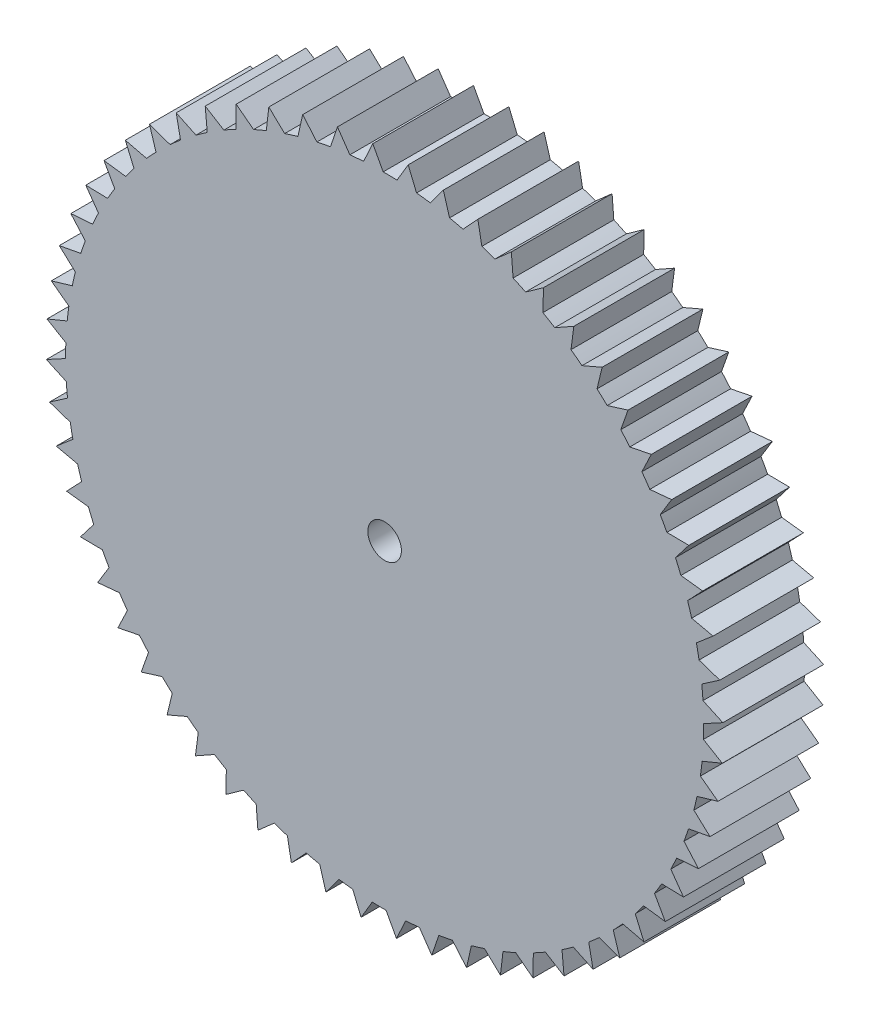
SolidWorks part; units mm, degrees
ref_plane "Front Plane" through (0, 0, 0) normal (0, 0, 1) x (1, 0, 0)
ref_plane "Top Plane" through (0, 0, 0) normal (0, 1, 0) x (1, 0, 0)
ref_plane "Right Plane" through (0, 0, 0) normal (1, 0, 0) x (0, 0, -1)
sketch "Sketch2" plane through (0, 0, 0) normal (0, 1, 0) x (1, 0, 0)
  line L1 (0, 19.1406) -> (0, 42.1406)
  line L2 (21.9625, 25.9706) -> (-21.9625, 25.9706)
  circle A0 centre (0, 19.1406) radius 23
  point P1 (0, 25.9706)
  point P7 (0, 25.9706)
  dimension "D1" = 16.17
  dimension "D2" = 46
ref_plane "Plane1" through (0, 0, -25.9706) normal (0, 0, -1) x (-1, 0, 0)
sketch "Sketch3" plane through (0, 0, -25.9706) normal (0, 0, -1) x (-1, 0, 0)
  line L0 (21.9625, 0) -> (-21.9625, 0)
  line L1 (21.9625, 0) -> (21.9625, 85)
  line L2 (-21.9625, 0) -> (-21.9625, 85)
  line L3 (21.9625, 85) -> (-21.9625, 85)
  line L4 (21.9625, 0) -> (-21.9625, 85) construction
  line L5 (-21.9625, 0) -> (21.9625, 85) construction
  line L9 (34.4493, 57.3155) -> (18.9158, 10.4622)
  line L10 (32.1526, 56.3278) -> (13.3127, 12.5933)
  line L11 (-26.4622, 69.0707) -> (-24.6744, 67.3228)
  line L12 (0, 0) -> (0, 85)
  arc A0 (-24.6744, 67.3228) -> (32.1526, 56.3278) centre (0, 42.5) cw
  arc A1 (23.9765, 17.0024) -> (8.6581, 8.5878) centre (0, 42.5) cw
  arc A2 (-26.4622, 69.0707) -> (34.4493, 57.3155) centre (0, 42.5) cw
  circle A3 centre (16.0681, 11.4063) radius 2
  arc A4 (13.3127, 12.5933) -> (18.9158, 10.4622) centre (16.0681, 11.4063) ccw
  circle A5 centre (0, 42.5) radius 33.5
  circle A6 centre (0, 66.2) radius 9.5
  point P6 (0, 42.5)
  point P10 (16.0681, 11.4063)
  point P13 (-21.9625, 69.7516)
  point P23 (0, 42.5)
  point P26 (0, 76)
  point P27 (0, 75.7)
  point P28 (0.23, 75.6972)
  point P29 (-1.319, 75.608)
  point P31 (0, 73.5)
  dimension "D2" = 5.8944
  dimension "D4" = 0.3
  dimension "D5" = 67
  dimension "D6" = 19
  dimension "D1" = 85
  dimension "D3" = 15.2484
  dimension "D7" = 7.3
extrude "Boss-Extrude1" add sketch "Sketch3" along normal blind 3
sketch "Sketch7" plane through (0, 0, -28.9706) normal (0, 0, -1) x (-1, 0, 0)
  circle A0 centre (0, 66.2) radius 2
extrude "Boss-Extrude4" add sketch "Sketch7" along normal blind 3
sketch "Sketch8" plane through (0, 0, -31.9706) normal (0, 0, -1) x (-1, 0, 0)
  line L0 (0.4, 64.4) -> (-0.4, 64.4)
  line L2 (-0.4, 64.4) -> (0, 63.6)
  line L3 (0, 0) -> (0, 85) construction
  line L4 (0, 63.6) -> (0.4, 64.4)
  point P3 (0, 64.4)
  dimension "D1" = 1.8
  dimension "D2" = 0.8
  dimension "D3" = 0.8
extrude "Boss-Extrude5" add sketch "Sketch8" against normal blind 3
pattern_circular "CirPattern2" count 20 over 360 about axis through (0, 66.1682, 0) along (0, 0, 1) of "Boss-Extrude5"
sketch "Sketch9" plane through (0, 0, -31.9706) normal (0, 0, -1) x (-1, 0, 0)
  circle A0 centre (0, 66.2) radius 0.5
extrude "Cut-Extrude1" cut sketch "Sketch9" against normal blind 6
sketch "Sketch10" plane through (0, 0, -25.9706) normal (0, 0, 1) x (1, 0, 0)
  line L0 (0, 75.7) -> (1.319, 75.608)
  line L1 (0.6595, 75.654) -> (0, 66.2)
  line L2 (0.2456, 75.4851) -> (1.0456, 75.4229)
  line L3 (1.0456, 75.4229) -> (0.7014, 76.254)
  line L4 (0.7014, 76.254) -> (0.2456, 75.4851)
  line L5 (0.7014, 76.254) -> (0.6595, 75.654)
  point P10 (0.6456, 75.454)
  circle M5 centre (0, 66.2) radius 9.5
  dimension "D1" = 0.8
  dimension "D2" = 0.8
  dimension "D3" = 0.2
extrude "Boss-Extrude6" add sketch "Sketch10" against normal blind 3 contours L5 L4 M5 | L3 L5 M5
pattern_circular "CirPattern3" count 60 over 360 about axis through (0, 66.2, 0) along (0, 0, 1) of "Boss-Extrude6"
